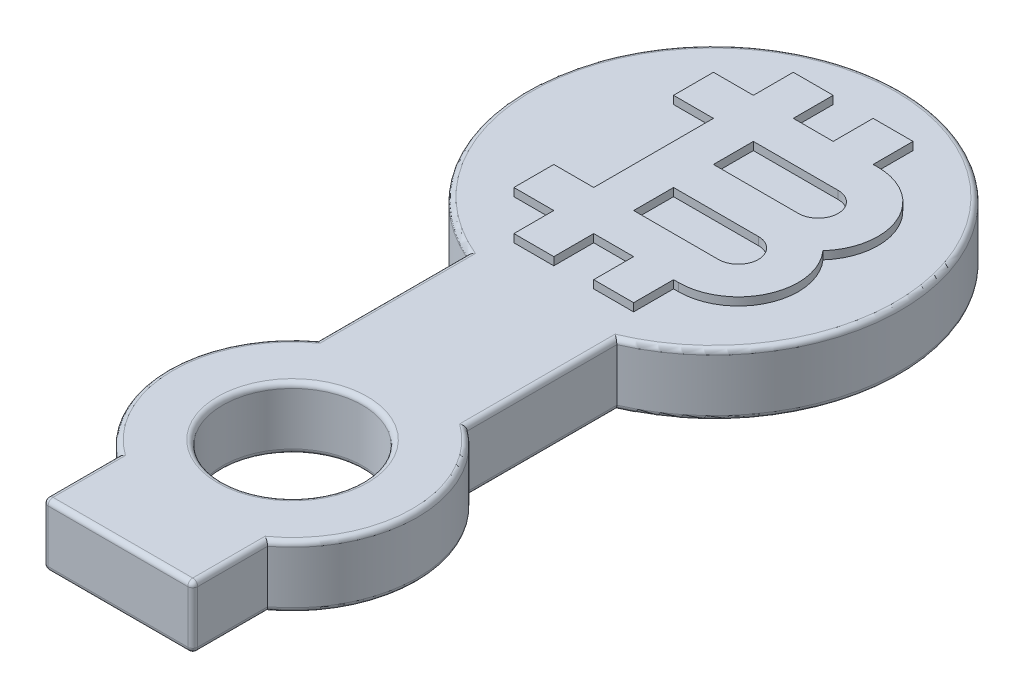
SolidWorks part; units mm, degrees
ref_plane "前视基准面" through (0, 0, 0) normal (0, 0, 1) x (1, 0, 0)
ref_plane "上视基准面" through (0, 0, 0) normal (0, 1, 0) x (1, 0, 0)
ref_plane "右视基准面" through (0, 0, 0) normal (1, 0, 0) x (0, 0, -1)
other "Configuration Table"
sketch "草图4" plane through (0, 0, 0) normal (0, 1, 0) x (1, 0, 0)
  line L0 (-3, 4) -> (-3, 10)
  line L2 (3, 10) -> (3, 4)
  line L3 (-3, -4) -> (-3, -7)
  line L4 (-3, -7) -> (3, -7)
  line L5 (3, -7) -> (3, -4)
  line L6 (0, 0) -> (0, 16.8739) construction
  circle A0 centre (0, 0) radius 2.8
  circle A1 centre (0, 0) radius 5
  circle A2 centre (0, 16.8739) radius 7.5
  dimension "D1" = 5.6
  dimension "D2" = 10
  dimension "D3" = 15
  dimension "D4" = 6
  dimension "D5" = 3
  dimension "D6" = 6
extrude "凸台-拉伸2" add sketch "草图4" along normal blind 2.5
fillet "圆角1" radius 0.2 20 edges at (0, 2.5, 2.8) (0, 0, 2.8) (-5, 0, 0) (-5, 2.5, 0) (-3, 0, 5.5) (-3, 2.5, 5.5) (0, 0, 7) (0, 2.5, 7) (3, 0, 5.5) (3, 2.5, 5.5) (5, 0, 0) (5, 2.5, 0) (3, 0, -7) (3, 2.5, -7) (0, 0, -24.3739) (0, 2.5, -24.3739) (-3, 0, -7) (-3, 2.5, -7) (3, 1.25, 7) (-3, 1.25, 7)
sketch "草图1" plane through (0, 2.5, 0) normal (0, 1, 0) x (1, 0, 0)
  line L1 (-15.5883, 16.8739) -> (31.6232, 16.8739) construction
  line L2 (-0.8, 17.6739) -> (2.6, 17.6739)
  line L3 (-0.8, 17.6739) -> (-0.8, 19.2739)
  line L4 (-0.8, 19.2739) -> (2.6, 19.2739)
  line L5 (2.6, 16.0739) -> (-0.8, 16.0739)
  line L6 (-0.8, 16.0739) -> (-0.8, 14.4739)
  line L7 (-0.8, 14.4739) -> (2.6, 14.4739)
  line L9 (-0.8, 22.4739) -> (-2.4, 22.4739)
  line L10 (-2.4, 22.4739) -> (-2.4, 20.8739)
  line L11 (-2.4, 20.8739) -> (-4, 20.8739)
  line L12 (-4, 20.8739) -> (-4, 19.2739)
  line L13 (-4, 19.2739) -> (-2.4, 19.2739)
  line L14 (-2.4, 19.2739) -> (-2.4, 14.4739)
  line L15 (-4, 14.4739) -> (-4, 12.8739)
  line L16 (-4, 12.8739) -> (-2.4, 12.8739)
  line L17 (-2.4, 14.4739) -> (-4, 14.4739)
  line L18 (2.4, 20.8739) -> (2.6, 20.8739)
  line L19 (-2.4, 12.8739) -> (-2.4, 11.2739)
  line L20 (-2.4, 11.2739) -> (-0.8, 11.2739)
  line L22 (2.4, 12.8739) -> (2.6, 12.8739)
  line L23 (-0.8, 22.4739) -> (-0.8, 20.8739)
  line L24 (-0.8, 20.8739) -> (0.8, 20.8739)
  line L25 (0.8, 20.8739) -> (0.8, 22.4739)
  line L26 (0.8, 22.4739) -> (2.4, 22.4739)
  line L28 (2.4, 12.8739) -> (2.4, 11.2739)
  line L29 (2.4, 11.2739) -> (0.8, 11.2739)
  line L30 (0.8, 11.2739) -> (0.8, 12.8739)
  line L31 (0.8, 12.8739) -> (-0.8, 12.8739)
  line L32 (-0.8, 12.8739) -> (-0.8, 11.2739)
  line L33 (2.4, 20.8739) -> (2.4, 22.4739)
  arc A0 (2.6, 19.2739) -> (2.6, 17.6739) centre (2.6, 18.4739) cw
  arc A1 (2.6, 16.0739) -> (2.6, 14.4739) centre (2.6, 15.2739) cw
  arc A2 (2.6, 20.8739) -> (4.3889, 16.8739) centre (2.6, 18.4739) cw
  arc A3 (2.6, 12.8739) -> (4.3889, 16.8739) centre (2.6, 15.2739) ccw
  arc A4 (-3, 10) -> (3, 23.7477) centre (0, 16.8739) ccw construction
  arc A5 (-3, 10) -> (3, 23.7477) centre (0, 16.8739) ccw construction
  point P69 (0, 20.8739)
  dimension "D1" = 1.6
  dimension "D2" = 1.6
  dimension "D3" = 1.6
  dimension "D4" = 1.6
  dimension "D5" = 1.6
  dimension "D6" = 1.6
  dimension "D7" = 1.6
  dimension "D8" = 1.6
  dimension "D9" = 1.6
  dimension "D10" = 1.6
  dimension "D11" = 1.6
  dimension "D13" = 0.2
extrude "凸台-拉伸3" add sketch "草图1" along normal blind 0.32
equation "\"btc_min_width\"= 1.6mm"
equation "\"D1@草图1\"=\"btc_min_width\""
equation "\"D8@草图1\"=\"btc_min_width\""
equation "\"D11@草图1\"=\"btc_min_width\""
equation "\"D9@草图1\"=\"btc_min_width\""
equation "\"D2@草图1\"=\"btc_min_width\""
equation "\"D6@草图1\"=\"btc_min_width\""
equation "\"D4@草图1\"=\"btc_min_width\""
equation "\"D3@草图1\"=\"btc_min_width\""
equation "\"D5@草图1\"=\"btc_min_width\""
equation "\"D7@草图1\"=\"btc_min_width\""
equation "\"D10@草图1\"=\"btc_min_width\""
